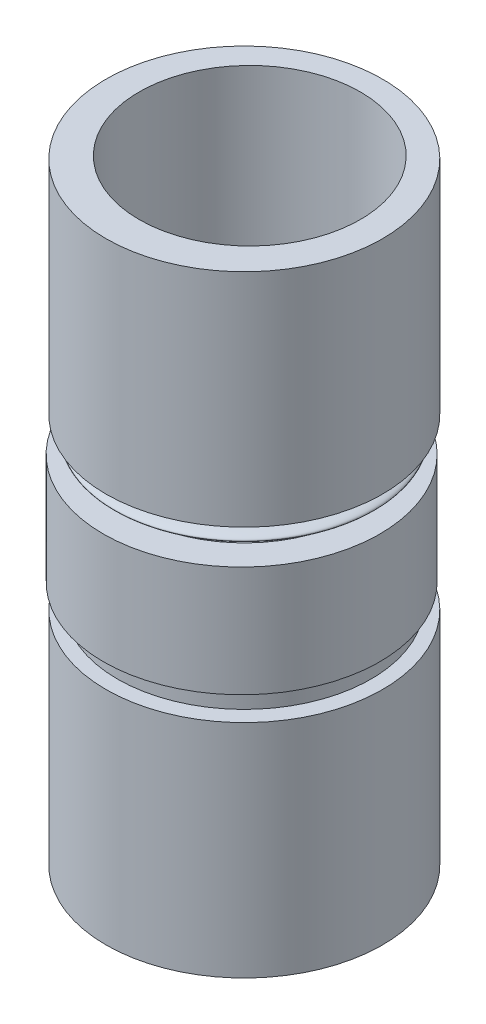
SolidWorks part; units mm, degrees
ref_plane "前视基准面" through (0, 0, 0) normal (0, 0, 1) x (1, 0, 0)
ref_plane "上视基准面" through (0, 0, 0) normal (0, 1, 0) x (1, 0, 0)
ref_plane "右视基准面" through (0, 0, 0) normal (1, 0, 0) x (0, 0, -1)
sketch "草图2" plane through (0, 0, 0) normal (0, 1, 0) x (1, 0, 0)
  circle A0 centre (0, 0) radius 6.25
  circle A1 centre (0, 0) radius 5
  dimension "D1" = 12.5
  dimension "D2" = 10
extrude "凸台-拉伸1" add sketch "草图2" along normal blind 10
sketch "草图3" plane through (0, 10, 0) normal (0, 1, 0) x (1, 0, 0)
  circle A0 centre (0, 0) radius 5.7316
extrude "凸台-拉伸2" add sketch "草图3" along normal blind 0.75 from offset 0.15 contours A0
sketch "草图4" plane through (0, 10.9, 0) normal (0, 1, 0) x (1, 0, 0)
  circle A0 centre (0, 0) radius 5
  circle A1 centre (0, -0.1216) radius 6.25
  dimension "D1" = 10
  dimension "D2" = 12.5
extrude "凸台-拉伸3" add sketch "草图4" along normal blind 5 from offset 0.25
sketch "草图5" plane through (0, 0, 0) normal (0, 0, 1) x (1, 0, 0)
  line L0 (0, 0) -> (0, 22.1108) construction
  line L1 (5, 16.15) -> (-5, 16.15) construction
  line L2 (0, 17.6644) -> (0, 16.15)
  line L3 (5.8532, 16.9072) -> (0, 16.9072)
  spline S0 degree 2 poles (0, 16.15) (11.7578, 16.8067) (0, 17.6644) knots 0 0 0 1 1 1
  point P5 (5.8532, 16.9072)
  point P9 (0, 16.8561)
  point P10 (0, 16.9072)
  point P11 (5.8532, 16.9072)
revolve "旋转1" add sketch "草图5" angle 360 about L0
sketch "草图6" plane through (0, 16.15, 0) normal (0, 1, 0) x (1, 0, 0)
  circle A0 centre (0, 0) radius 6.25
  circle A1 centre (0, 0.2472) radius 5
  dimension "D1" = 10
  dimension "D2" = 12.5
extrude "凸台-拉伸4" add sketch "草图6" along normal blind 10 from offset 1.5 separate body
